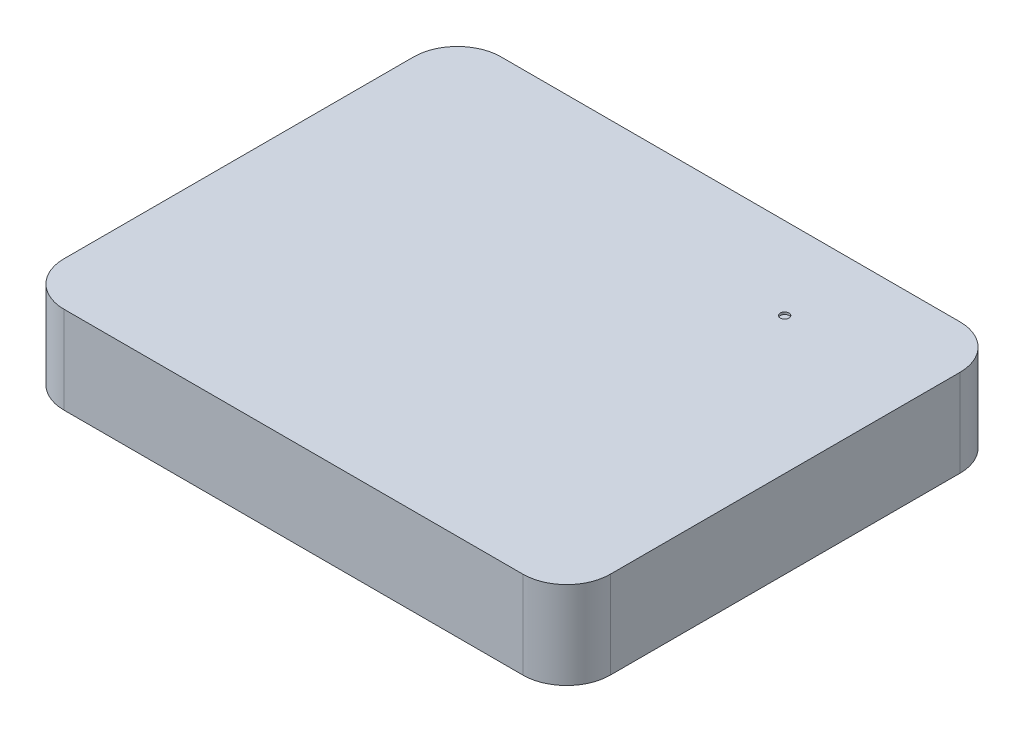
SolidWorks part; units mm, degrees
ref_plane "Front Plane" through (0, 0, 0) normal (0, 0, 1) x (1, 0, 0)
ref_plane "Top Plane" through (0, 0, 0) normal (0, 1, 0) x (1, 0, 0)
ref_plane "Right Plane" through (0, 0, 0) normal (1, 0, 0) x (0, 0, -1)
sketch "Sketch1" plane through (0, 0, 0) normal (0, 1, 0) x (1, 0, 0)
  line L1 (105, -100) -> (-105, -100)
  line L2 (125, -80) -> (125, 80)
  line L3 (105, 100) -> (-105, 100)
  line L4 (-125, -80) -> (-125, 80)
  line L5 (125, -100) -> (-125, 100) construction
  line L6 (125, 100) -> (-125, -100) construction
  arc A0 (-105, 100) -> (-125, 80) centre (-105, 80) ccw
  arc A1 (-105, -100) -> (-125, -80) centre (-105, -80) cw
  arc A2 (105, -100) -> (125, -80) centre (105, -80) ccw
  arc A3 (125, 80) -> (105, 100) centre (105, 80) ccw
  point P0 (0, 0)
  dimension "D3" = 20
  dimension "D1" = 200
  dimension "D2" = 250
extrude "Boss-Extrude1" add sketch "Sketch1" along normal blind 40
sketch "Sketch2" plane through (0, 40, 0) normal (0, 1, 0) x (1, 0, 0)
  circle A0 centre (62.3675, 62.3675) radius 2
  point P2 (62.3675, 62.3675)
  dimension "D1" = 4
extrude "Cut-Extrude1" cut sketch "Sketch2" against normal blind 1
